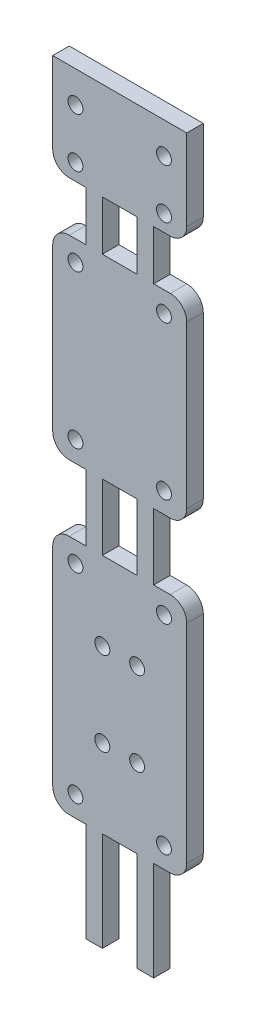
SolidWorks part; units mm, degrees
ref_plane "Front Plane" through (0, 0, 0) normal (0, 0, 1) x (1, 0, 0)
ref_plane "Top Plane" through (0, 0, 0) normal (0, 1, 0) x (1, 0, 0)
ref_plane "Right Plane" through (0, 0, 0) normal (1, 0, 0) x (0, 0, -1)
sketch "Sketch1" plane through (0, 0, 0) normal (0, 0, 1) x (1, 0, 0)
  line L0 (4, 26) -> (2, 26)
  line L1 (0, 1.5) -> (16.2, 1.5) construction
  line L2 (0, 14) -> (4, 14) construction
  line L3 (0, 14) -> (0, 1.5) construction
  line L4 (6, 14) -> (6, 26)
  line L5 (4, 14) -> (4, 26)
  line L6 (0, 28) -> (0, 53.14)
  line L7 (0, 94.665) -> (0, 104.46)
  line L8 (6, 14) -> (10.2, 14) construction
  line L9 (8.1, 1.5) -> (8.1, 104.46) construction
  line L10 (0, 104.46) -> (16.2, 104.46)
  line L11 (6, 63.14) -> (10.2, 63.14)
  line L12 (6, 55.14) -> (10.2, 55.14)
  line L13 (6, 92.665) -> (10.2, 92.665)
  line L14 (6, 86.665) -> (10.2, 86.665)
  line L15 (16.2, 84.665) -> (16.2, 65.14)
  line L16 (10.2, 86.665) -> (10.2, 92.665)
  line L17 (14.2, 55.14) -> (12.2, 55.14)
  line L18 (2, 92.665) -> (4, 92.665)
  line L19 (2, 86.665) -> (4, 86.665)
  line L20 (2, 63.14) -> (4, 63.14)
  line L21 (10.2, 55.14) -> (10.2, 63.14)
  line L22 (4, 86.665) -> (4, 92.665)
  line L23 (4, 55.14) -> (4, 63.14)
  line L24 (6, 55.14) -> (6, 63.14)
  line L25 (2, 55.14) -> (4, 55.14)
  line L26 (6, 86.665) -> (6, 92.665)
  line L27 (12.2, 55.14) -> (12.2, 63.14)
  line L28 (12.2, 86.665) -> (12.2, 92.665)
  line L29 (14.2, 63.14) -> (12.2, 63.14)
  line L30 (14.2, 86.665) -> (12.2, 86.665)
  line L31 (14.2, 92.665) -> (12.2, 92.665)
  line L32 (6, 26) -> (10.2, 26)
  line L33 (4, 14) -> (6, 14)
  line L34 (16.2, 94.665) -> (16.2, 104.46)
  line L35 (16.2, 28) -> (16.2, 53.14)
  line L36 (12.2, 14) -> (12.2, 26)
  line L37 (10.2, 14) -> (10.2, 26)
  line L38 (16.2, 14) -> (16.2, 1.5) construction
  line L39 (16.2, 14) -> (12.2, 14) construction
  line L40 (12.2, 26) -> (14.2, 26)
  line L41 (10.2, 14) -> (12.2, 14)
  line L58 (0, 84.665) -> (0, 65.14)
  circle A0 centre (2.85, 11.5) radius 0.9 construction
  circle A1 centre (13.45, 94.665) radius 0.9
  circle A2 centre (13.45, 84.165) radius 0.9
  circle A3 centre (2.85, 5.5) radius 0.9 construction
  circle A4 centre (13.45, 65.64) radius 0.9
  circle A5 centre (13.45, 52.64) radius 0.9
  circle A6 centre (13.45, 28.5) radius 0.9
  circle A7 centre (10.2, 35.5) radius 0.9
  arc A8 (16.2, 28) -> (14.2, 26) centre (14.2, 28) cw
  circle A9 centre (10.2, 45.64) radius 0.9
  arc A10 (2, 86.665) -> (0, 84.665) centre (2, 84.665) ccw
  arc A11 (14.2, 55.14) -> (16.2, 53.14) centre (14.2, 53.14) cw
  circle A12 centre (13.45, 100.665) radius 0.9
  arc A13 (16.2, 94.665) -> (14.2, 92.665) centre (14.2, 94.665) cw
  arc A14 (16.2, 65.14) -> (14.2, 63.14) centre (14.2, 65.14) cw
  arc A15 (0, 65.14) -> (2, 63.14) centre (2, 65.14) ccw
  arc A16 (0, 94.665) -> (2, 92.665) centre (2, 94.665) ccw
  arc A17 (14.2, 86.665) -> (16.2, 84.665) centre (14.2, 84.665) cw
  circle A18 centre (2.75, 100.665) radius 0.9
  circle A19 centre (13.35, 5.5) radius 0.9 construction
  circle A20 centre (13.35, 11.5) radius 0.9 construction
  arc A22 (2, 55.14) -> (0, 53.14) centre (2, 53.14) ccw
  circle A24 centre (6, 45.64) radius 0.9
  arc A26 (0, 28) -> (2, 26) centre (2, 28) ccw
  circle A30 centre (6, 35.5) radius 0.9
  circle A32 centre (2.75, 28.5) radius 0.9
  circle A34 centre (2.75, 52.64) radius 0.9
  circle A36 centre (2.75, 65.64) radius 0.9
  circle A38 centre (2.75, 84.165) radius 0.9
  circle A40 centre (2.75, 94.665) radius 0.9
  point P9 (8.1, 92.665)
  point P11 (8.1, 86.665)
  point P16 (8.1, 63.14)
  point P17 (8.1, 55.14)
  point P20 (8.1, 63.14)
  point P21 (8.1, 55.14)
  point P58 (8.1, 26)
  point P66 (8.1, 14)
  point P83 (8.1, 26)
  point P96 (8.1, 92.665)
  point P100 (8.1, 14)
  dimension "D11" = 2.75
  dimension "D12" = 6
  dimension "D13" = 2.5
  dimension "D14" = 9.5
  dimension "D15" = 2.75
  dimension "D16" = 6
  dimension "D8" = 2
  dimension "D28" = 2
  dimension "D30" = 2
  dimension "D32" = 2
  dimension "D42" = 1.8
  dimension "D44" = 2
  dimension "D2" = 2.85
  dimension "D3" = 4
  dimension "D4" = 2.85
  dimension "D5" = 6
  dimension "D6" = 2.5
  dimension "D7" = 12
  dimension "D9" = 2.5
  dimension "D10" = 9.5
  dimension "D17" = 29.14
  dimension "D18" = 2.75
  dimension "D19" = 2.5
  dimension "D20" = 8
  dimension "D21" = 2
  dimension "D22" = 2
  dimension "D23" = 2
  dimension "D24" = 2
  dimension "D25" = 2.75
  dimension "D26" = 2.5
  dimension "D27" = 23.525
  dimension "D39" = 2
  dimension "D40" = 2.75
  dimension "D41" = 6
  dimension "D45" = 2.75
  dimension "D46" = 6
  dimension "D47" = 11.795
  dimension "D48" = 8.1
  dimension "D49" = 2
extrude "Boss-Extrude1" add sketch "Sketch1" along normal blind 2
sketch "Sketch2" plane through (0, 0, 2) normal (0, 0, 1) x (1, 0, 0)
  line L0 (4, 92.665) -> (12.2, 92.665)
  line L1 (12.2, 92.665) -> (12.2, 86.665)
  line L2 (12.2, 86.665) -> (4, 86.665)
  line L3 (4, 86.665) -> (4, 92.665)
  line L4 (4, 63.14) -> (12.2, 63.14)
  line L5 (12.2, 63.14) -> (12.2, 55.14)
  line L6 (12.2, 55.14) -> (4, 55.14)
  line L7 (4, 55.14) -> (4, 63.14)
  line L8 (4, 26) -> (12.2, 26)
  line L9 (12.2, 26) -> (12.2, 14)
  line L10 (12.2, 14) -> (4, 14)
  line L11 (4, 14) -> (4, 26)
extrude "Cut-Extrude1" [suppressed] cut sketch "Sketch2" against normal up to surface (2 mm away)
equation "\"D48@Sketch1\"= ( \"fingerWidth@parametersSketch@prostheticParameters.SLDPRT\" ) / 2 'Ring Width"
equation "\"D17@Sketch1\"= \"HL@parametersSketch@prostheticParameters.SLDPRT\" * 0.244 - 4 - 12'Ring PIP Length"
equation "\"D27@Sketch1\"= \"HL@parametersSketch@prostheticParameters.SLDPRT\" * 0.165 - 3 - 4'Ring MIP Length"
equation "\"D47@Sketch1\"= \"HL@parametersSketch@prostheticParameters.SLDPRT\" * 0.107 - 3 - 5'Ring DIP Length - Gap fingertip"
equation "\"D42@Sketch1\"= 1.5 + \"tol1@parametersSketch@prostheticParameters.SLDPRT\""
